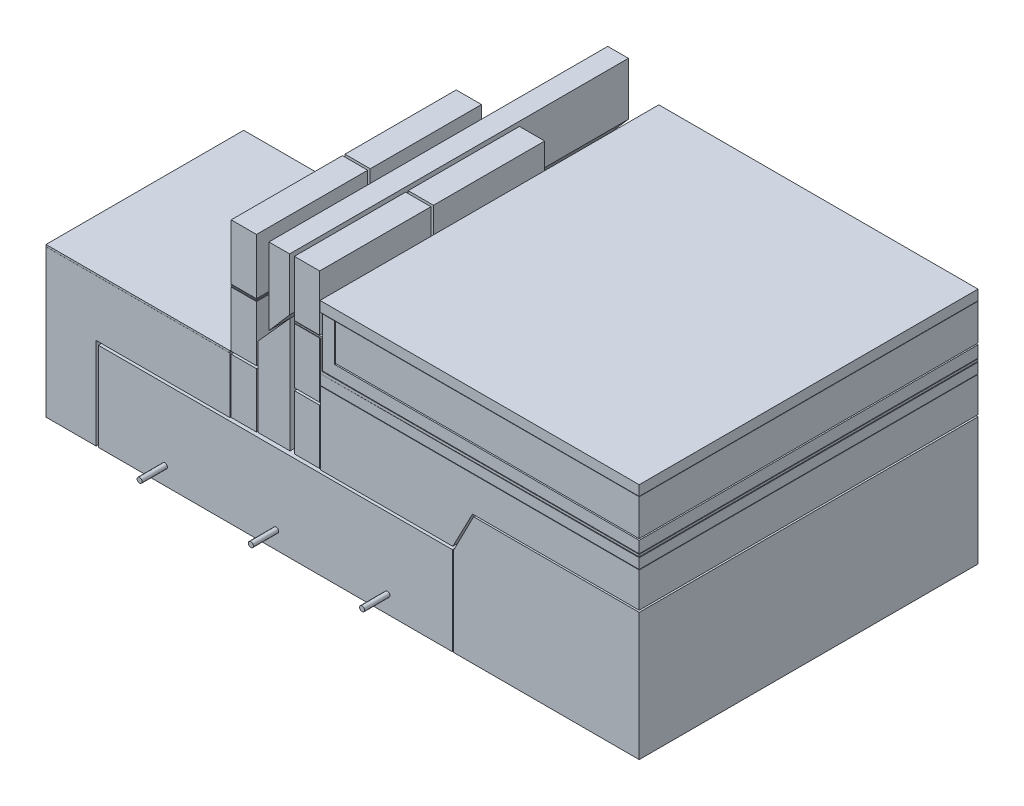
SolidWorks part; units mm, degrees
ref_plane "Front" through (0, 0, 0) normal (0, 0, 1) x (1, 0, 0)
ref_plane "Top" through (0, 0, 0) normal (0, 1, 0) x (1, 0, 0)
ref_plane "Right" through (0, 0, 0) normal (1, 0, 0) x (0, 0, -1)
sketch "Sketch2" plane through (0, 0, 0) normal (0, 0, 1) x (1, 0, 0)
  line L0 (0, 0) -> (0, 350) construction
  line L1 (-700, 365.1993) -> (-600, 365.1993)
  line L2 (-700, 365.1993) -> (-700, 582.0932)
  line L3 (-700, 582.0932) -> (-600, 582.0932)
  line L4 (-600, 365.1993) -> (-600, 582.0932)
  line L5 (-450, 365.1993) -> (-350, 365.1993)
  line L6 (-450, 365.1993) -> (-450, 582.0932)
  line L7 (-450, 582.0932) -> (-350, 582.0932)
  line L8 (-350, 365.1993) -> (-350, 582.0932)
  dimension "D1" = 150
  dimension "D2" = 100
  dimension "D3" = 100
  dimension "D4" = 350
extrude "Extrude2" add sketch "Sketch2" against normal blind 440 separate body
sketch "Sketch3" plane through (-700, 0, 0) normal (-1, 0, 0) x (0, 0, 1)
  line L0 (-440, 582.0932) -> (-440, 365.1993) construction
  line L1 (-450, 582.0932) -> (-890, 582.0932)
  line L2 (-450, 582.0932) -> (-450, 362.0932)
  line L3 (-450, 362.0932) -> (-890, 362.0932)
  line L4 (-890, 582.0932) -> (-890, 362.0932)
  line L6 (-900, 582.0932) -> (-1340, 582.0932)
  line L7 (-900, 582.0932) -> (-900, 362.0932)
  line L8 (-900, 362.0932) -> (-1340, 362.0932)
  line L9 (-1340, 582.0932) -> (-1340, 362.0932)
  dimension "D1" = 440
  dimension "D2" = 220
  dimension "D3" = 10
  dimension "D4" = 440
  dimension "D5" = 220
  dimension "D6" = 10
extrude "Extrude3" add sketch "Sketch3" against normal blind 100 separate body
sketch "Sketch4" plane through (-350, 0, 0) normal (1, 0, 0) x (0, 0, -1)
  line L1 (450, 582.0932) -> (890, 582.0932)
  line L2 (450, 582.0932) -> (450, 362.0932)
  line L3 (450, 362.0932) -> (890, 362.0932)
  line L4 (890, 582.0932) -> (890, 362.0932)
  line L5 (1340, 582.0932) -> (900, 582.0932)
  line L6 (1340, 582.0932) -> (1340, 362.0932)
  line L7 (1340, 362.0932) -> (900, 362.0932)
  line L8 (900, 582.0932) -> (900, 362.0932)
extrude "Extrude4" add sketch "Sketch4" against normal blind 100 separate body
sketch "Sketch6" plane through (-700, 0, 0) normal (-1, 0, 0) x (0, 0, 1)
  line L0 (-440, 582.0932) -> (0, 582.0932) construction
  line L1 (0, 592.0932) -> (-215, 592.0932)
  line L2 (0, 592.0932) -> (0, 812.0932)
  line L3 (0, 812.0932) -> (-215, 812.0932)
  line L4 (-215, 592.0932) -> (-215, 812.0932)
  line L5 (0, 582.0932) -> (0, 365.1993) construction
  line L6 (-225, 812.0932) -> (-670.705, 812.0932)
  line L7 (-225, 812.0932) -> (-225, 592.0932)
  line L8 (-225, 592.0932) -> (-670.705, 592.0932)
  line L9 (-670.705, 812.0932) -> (-670.705, 592.0932)
  line L11 (-680.705, 812.0932) -> (-1120.705, 812.0932)
  line L12 (-680.705, 812.0932) -> (-680.705, 592.0932)
  line L13 (-680.705, 592.0932) -> (-1120.705, 592.0932)
  line L14 (-1120.705, 812.0932) -> (-1120.705, 592.0932)
  dimension "D1" = 215
  dimension "D2" = 220
  dimension "D3" = 10
  dimension "D4" = 445.705
  dimension "D5" = 10
  dimension "D6" = 440
  dimension "D7" = 220
  dimension "D8" = 10
extrude "Extrude6" add sketch "Sketch6" against normal blind 100 separate body
sketch "Sketch7" plane through (-350, 0, 0) normal (1, 0, 0) x (0, 0, -1)
  line L1 (0, 812.0932) -> (215, 812.0932)
  line L2 (0, 812.0932) -> (0, 592.0932)
  line L3 (0, 592.0932) -> (215, 592.0932)
  line L4 (215, 812.0932) -> (215, 592.0932)
  line L5 (670.705, 812.0932) -> (225, 812.0932)
  line L6 (670.705, 812.0932) -> (670.705, 592.0932)
  line L7 (670.705, 592.0932) -> (225, 592.0932)
  line L8 (225, 812.0932) -> (225, 592.0932)
  line L9 (1120.705, 812.0932) -> (680.705, 812.0932)
  line L10 (1120.705, 812.0932) -> (1120.705, 592.0932)
  line L11 (1120.705, 592.0932) -> (680.705, 592.0932)
  line L12 (680.705, 812.0932) -> (680.705, 592.0932)
extrude "Extrude7" add sketch "Sketch7" against normal blind 100 separate body
sketch "Sketch8" plane through (-700, 0, 0) normal (-1, 0, 0) x (0, 0, 1)
  line L1 (0, 822.0932) -> (-440, 822.0932)
  line L2 (0, 822.0932) -> (0, 1042.0932)
  line L3 (0, 1042.0932) -> (-440, 1042.0932)
  line L4 (-440, 822.0932) -> (-440, 1042.0932)
  line L5 (-450, 1042.0932) -> (-890, 1042.0932)
  line L6 (-450, 1042.0932) -> (-450, 822.0932)
  line L7 (-450, 822.0932) -> (-890, 822.0932)
  line L8 (-890, 1042.0932) -> (-890, 822.0932)
  line L9 (0, 592.0932) -> (0, 812.0932) construction
  line L10 (-225, 812.0932) -> (-670.705, 812.0932) construction
  dimension "D1" = 220
  dimension "D2" = 440
  dimension "D3" = 440
  dimension "D4" = 220
  dimension "D5" = 10
  dimension "D6" = 10
extrude "Extrude8" add sketch "Sketch8" against normal blind 100 separate body
sketch "Sketch9" plane through (-350, 0, 0) normal (1, 0, 0) x (0, 0, -1)
  line L0 (450, 822.0932) -> (450, 1042.0932) construction
  line L1 (0, 1042.0932) -> (440, 1042.0932)
  line L2 (0, 1042.0932) -> (0, 822.0932)
  line L3 (0, 822.0932) -> (440, 822.0932)
  line L4 (440, 1042.0932) -> (440, 822.0932)
  line L5 (890, 1042.0932) -> (450, 1042.0932)
  line L6 (890, 1042.0932) -> (890, 822.0932)
  line L7 (890, 822.0932) -> (450, 822.0932)
  line L8 (450, 1042.0932) -> (450, 822.0932)
  line L9 (890, 822.0932) -> (450, 822.0932) construction
extrude "Extrude9" add sketch "Sketch9" against normal blind 100 separate body
sketch "Sketch10" plane through (0, 0, 0) normal (0, 0, 1) x (1, 0, 0)
  circle A0 centre (-962.1446, 68.9019) radius 10
  circle A1 centre (-522.1446, 68.9019) radius 10
  circle A2 centre (-82.1446, 68.9019) radius 10
  dimension "D1" = 20
  dimension "D2" = 20
  dimension "D3" = 20
  dimension "D4" = 440
  dimension "D5" = 440
extrude "Extrude10" add sketch "Sketch10" along normal blind 100
sketch "Sketch11" plane through (0, 0, 0) normal (0, 0, 1) x (1, 0, 0)
  line L0 (-467.1426, 366.7602) -> (-467.1426, 821.0478)
  line L1 (-467.1426, 821.0478) -> (-593.7131, 680.0214)
  line L2 (-593.7131, 680.0214) -> (-593.7131, 366.7602)
  line L3 (-593.7131, 366.7602) -> (-467.1426, 366.7602)
extrude "Extrude11" add sketch "Sketch11" against normal up to vertex (1340 mm away) separate body
sketch "Sketch12" plane through (0, 0, 0) normal (0, 0, 1) x (1, 0, 0)
  line L0 (-468.8878, 831.9878) -> (-468.8878, 1040.9897)
  line L1 (-468.8878, 1040.9897) -> (-550.7167, 1040.9897)
  line L2 (-550.7167, 1040.9897) -> (-550.7167, 737.6058)
  line L3 (-550.7167, 737.6058) -> (-468.8878, 831.9878)
extrude "Extrude12" add sketch "Sketch12" against normal up to vertex (1340 mm away) separate body
sketch "Sketch13" plane through (0, 0, 0) normal (0, 0, 1) x (1, 0, 0)
  line L0 (-336.3604, 649.5375) -> (-346.2691, 649.5375)
  line L1 (-346.2691, 649.5375) -> (-346.2691, 361.9862)
  line L2 (254.4725, 511.6205) -> (913.6669, 511.6205)
  line L3 (913.6669, 511.6205) -> (913.6669, 649.5375)
  line L4 (913.6669, 649.5375) -> (-336.3604, 649.5375)
  line L5 (-346.2691, 361.9862) -> (176.5782, 361.9862)
  line L7 (176.5782, 361.9862) -> (254.4725, 511.6205)
extrude "Extrude13" add sketch "Sketch13" against normal up to vertex (1340 mm away) separate body
sketch "Sketch25" plane through (0, 0, 0) normal (0, 0, 1) x (1, 0, 0)
  line L1 (-346.3646, 651.5107) -> (913.7761, 651.5107)
  line L2 (-346.3646, 651.5107) -> (-346.3646, 691.5107)
  line L3 (-346.3646, 691.5107) -> (913.7761, 691.5107)
  line L4 (913.7761, 651.5107) -> (913.7761, 691.5107)
  dimension "D1" = 40
extrude "Extrude24" add sketch "Sketch25" against normal up to vertex (1340 mm away) separate body
sketch "Sketch19" plane through (0, 0, 0) normal (0, 0, 1) x (1, 0, 0)
  line L1 (-600.0803, 819.7616) -> (-700.0973, 819.7616)
  line L2 (-600.0803, 819.7616) -> (-600.0803, 815.3456)
  line L3 (-600.0803, 815.3456) -> (-700.0973, 815.3456)
  line L4 (-700.0973, 819.7616) -> (-700.0973, 815.3456)
sketch "Sketch26" plane through (0, 0, 0) normal (0, 0, 1) x (1, 0, 0)
  line L0 (-450, 820.129) -> (-341.1313, 820.129)
  line L1 (-341.1313, 820.129) -> (-341.1313, 702.6672)
  line L2 (-341.1313, 702.6672) -> (913.7761, 702.6672)
  line L3 (913.7761, 702.6672) -> (913.7761, 694.7292)
  line L4 (913.7761, 694.7292) -> (-346.3646, 691.5107)
  line L5 (-346.3646, 691.5107) -> (-346.3646, 651.5107) construction
  line L6 (913.7761, 691.5107) -> (-346.3646, 691.5107) construction
  line L7 (-346.3646, 691.5107) -> (-346.3646, 814.2209)
  line L8 (-346.3646, 814.2209) -> (-450, 814.2209)
  line L9 (-450, 814.2209) -> (-450, 820.129)
extrude "Extrude25" add sketch "Sketch26" against normal up to vertex (1340 mm away) separate body
extrude "Extrude26" add sketch "Sketch19" against normal up to vertex (1120.705 mm away) separate body
sketch "Sketch27" plane through (0, 0, 0) normal (0, 0, 1) x (1, 0, 0)
  line L0 (-291.1058, 751.2168) -> (-291.1058, 900.3629)
  line L1 (-291.1058, 900.3629) -> (-339.1626, 900.3629)
  line L2 (-339.1626, 900.3629) -> (-339.1626, 705.1945)
  line L3 (-291.1058, 751.2168) -> (913.7761, 751.2168)
  line L4 (913.7761, 751.2168) -> (913.7761, 705.1945)
  line L5 (913.7761, 705.1945) -> (-339.1626, 705.1945)
extrude "Extrude27" add sketch "Sketch27" against normal up to vertex (1340 mm away) separate body
sketch "Sketch28" plane through (0, 0, 0) normal (0, 0, 1) x (1, 0, 0)
  line L1 (-287.4831, 900.3629) -> (913.7761, 900.3629)
  line L2 (-287.4831, 900.3629) -> (-287.4831, 756.795)
  line L3 (-287.4831, 756.795) -> (913.7761, 756.795)
  line L4 (913.7761, 900.3629) -> (913.7761, 756.795)
extrude "Extrude28" add sketch "Sketch28" against normal up to vertex (1340 mm away) separate body
sketch "Sketch29" plane through (0, 0, 0) normal (0, 0, 1) x (1, 0, 0)
  line L1 (-348.6584, 901.7939) -> (913.7761, 901.7939)
  line L2 (-348.6584, 901.7939) -> (-348.6584, 941.7939)
  line L3 (-348.6584, 941.7939) -> (913.7761, 941.7939)
  line L4 (913.7761, 901.7939) -> (913.7761, 941.7939)
  dimension "D1" = 40
extrude "Extrude29" add sketch "Sketch29" against normal up to vertex (1340 mm away) separate body
sketch "Sketch20" plane through (0, 0, 0) normal (0, 0, 1) x (1, 0, 0)
  line L0 (-700, 582.0932) -> (-700, 365.1993) construction
  line L1 (-1225, 350) -> (175, 350)
  line L2 (-1225, 350) -> (-1225, 0)
  line L3 (-1225, 0) -> (175, 0)
  line L4 (175, 350) -> (175, 0)
  dimension "D1" = 1400
  dimension "D2" = 525
extrude "Extrude20" add sketch "Sketch20" against normal blind 1400
sketch "Sketch21" plane through (0, 0, 0) normal (0, 0, 1) x (1, 0, 0)
  line L0 (-705.1392, 362.0265) -> (-705.1392, 583.6836)
  line L1 (-705.1392, 583.6836) -> (-1432.4688, 583.6836)
  line L2 (-1432.4688, 583.6836) -> (-1432.4688, 0)
  line L3 (-1432.4688, 0) -> (-1234.1314, 0)
  line L4 (-1234.1314, 0) -> (-1234.1314, 362.0265)
  line L5 (-1234.1314, 362.0265) -> (-705.1392, 362.0265)
extrude "Extrude21" add sketch "Sketch21" against normal blind 782 separate body
sketch "Sketch22" plane through (0, 0, 0) normal (0, 0, 1) x (1, 0, 0)
  line L1 (-1432.4688, 583.8864) -> (-705.1665, 583.8864)
  line L2 (-1432.4688, 583.8864) -> (-1432.4688, 591.552)
  line L3 (-1432.4688, 591.552) -> (-705.1665, 591.552)
  line L4 (-705.1665, 583.8864) -> (-705.1665, 591.552)
extrude "Extrude22" add sketch "Sketch22" against normal up to vertex (782 mm away) separate body
sketch "Sketch24" plane through (0, 0, 0) normal (0, 0, 1) x (1, 0, 0)
  line L0 (179.9095, 0) -> (179.9095, 350.525)
  line L1 (179.9095, 350.525) -> (258.843, 504.4232)
  line L2 (258.843, 504.4232) -> (913.8017, 504.4232)
  line L3 (913.8017, 504.4232) -> (913.8017, 0)
  line L4 (913.8017, 0) -> (179.9095, 0)
extrude "Extrude23" add sketch "Sketch24" against normal up to vertex (1340 mm away) separate body
